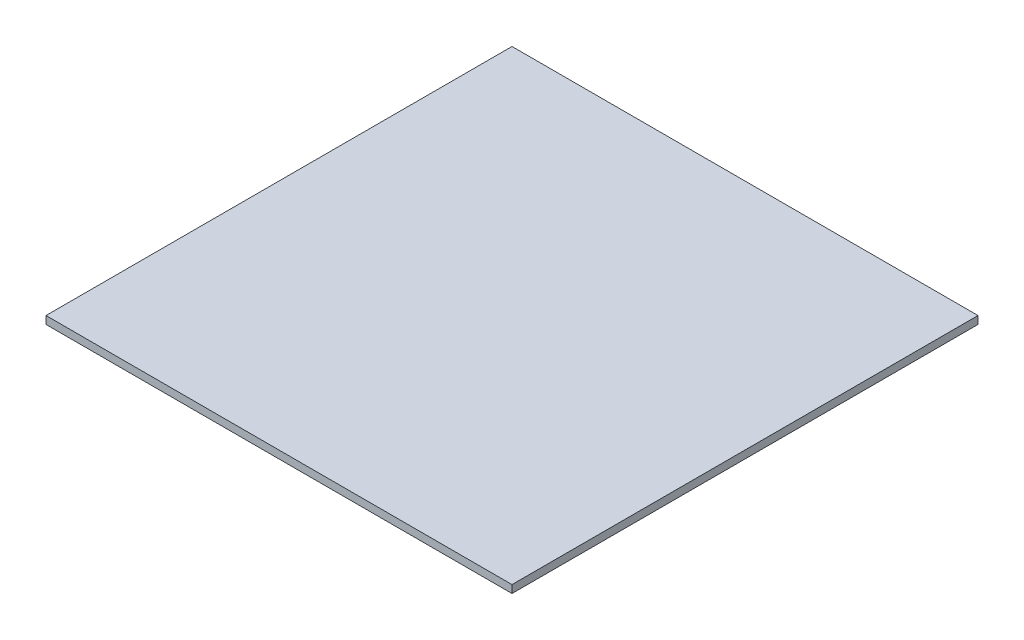
SolidWorks part; units mm, degrees
ref_plane "Face" through (0, 0, 0) normal (0, 0, 1) x (1, 0, 0)
ref_plane "Dessus" through (0, 0, 0) normal (0, 1, 0) x (1, 0, 0)
ref_plane "Droite" through (0, 0, 0) normal (1, 0, 0) x (0, 0, -1)
sketch "Esquisse1" plane through (0, 0, 0) normal (0, 1, 0) x (1, 0, 0)
  line L1 (0, 0) -> (300, 0)
  line L2 (0, 0) -> (0, 300)
  line L3 (0, 300) -> (300, 300)
  line L4 (300, 0) -> (300, 300)
  dimension "D1" = 300
  dimension "D2" = 300
extrude "Extrusion1" add sketch "Esquisse1" along normal blind 5
